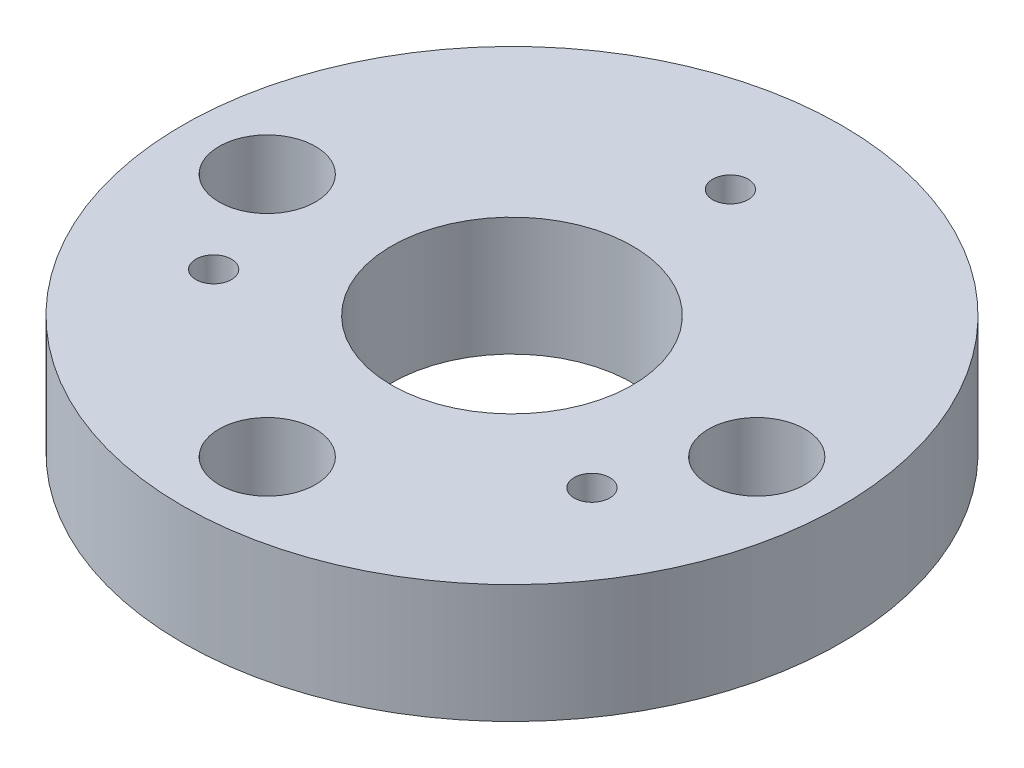
SolidWorks part; units mm, degrees
ref_plane "Front" through (0, 0, 0) normal (0, 0, 1) x (1, 0, 0)
ref_plane "Top" through (0, 0, 0) normal (0, 1, 0) x (1, 0, 0)
ref_plane "Right" through (0, 0, 0) normal (1, 0, 0) x (0, 0, -1)
sketch "Sketch1" plane through (0, 0, 0) normal (0, 1, 0) x (1, 0, 0)
  circle A0 centre (0, 0) radius 27.7876
  circle A1 centre (0, 0) radius 10.16
  dimension "D1" = 20.32
  dimension "D2" = 55.5752
extrude "Ring" add sketch "Sketch1" along normal blind 10
sketch "Sketch2" plane through (0, 10, 0) normal (0, 1, 0) x (1, 0, 0)
  circle A0 centre (0, 18.415) radius 1.5
  circle A1 centre (15.9479, -9.2075) radius 1.5
  circle A2 centre (-15.9479, -9.2075) radius 1.5
  point P8 (0, 0)
  dimension "D3" = 3
  dimension "D2" = 18.415
  dimension "D1" = 3
extrude "Robot Side1 - Holes" cut sketch "Sketch2" against normal through all
chamfer "Robot Side - Chamfer" distance 2.4 angle 45 3 edges at (-15.9479, 0, 10.7075) (15.9479, 0, 10.7075) (0, 0, -16.915)
sketch "Sketch3" plane through (0, 10, 0) normal (0, 1, 0) x (1, 0, 0)
  circle A0 centre (20.6375, 0) radius 1.8387
  circle A1 centre (0, -20.6375) radius 1.8387
  circle A2 centre (-20.6375, 0) radius 1.8387
  point P11 (0, 0)
  dimension "D2" = 20.6375
extrude "Tool Side - Holes" cut sketch "Sketch3" against normal through all
sketch "Sketch4" plane through (0, 10, 0) normal (0, 1, 0) x (1, 0, 0)
  circle A0 centre (-20.6375, 0) radius 4.064
  circle A1 centre (0, -20.6375) radius 4.064
  circle A2 centre (20.6375, 0) radius 4.064
  dimension "D1" = 8.128
  dimension "D2" = 8.128
  dimension "D3" = 8.128
extrude "Tool Side - Inset" cut sketch "Sketch4" against normal blind 6
equation "\"D2@Sketch4\"=\"D1@Sketch4\""
equation "\"D3@Sketch4\"=\"D1@Sketch4\""
